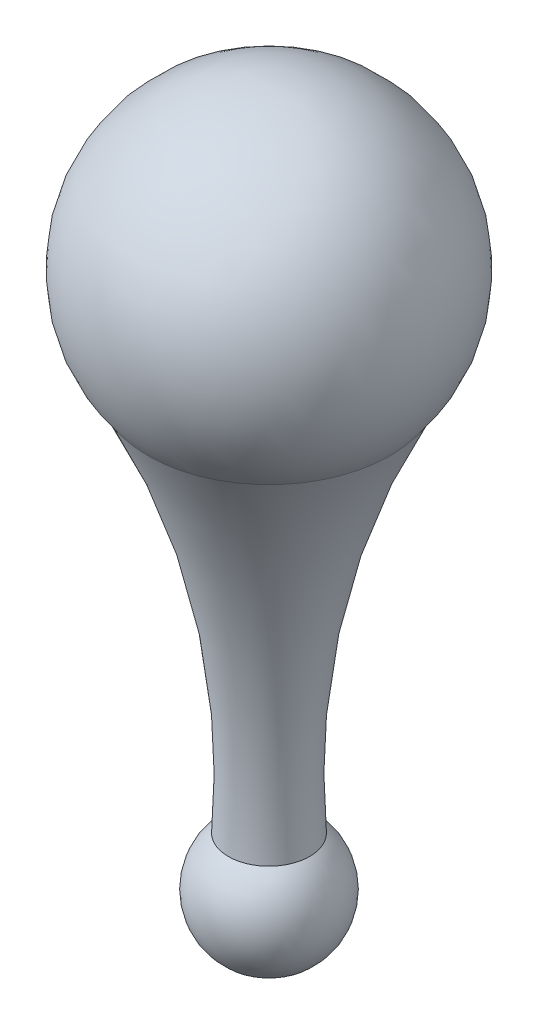
SolidWorks part; units mm, degrees
ref_plane "Front Plane" through (0, 0, 0) normal (0, 0, 1) x (1, 0, 0)
ref_plane "Top Plane" through (0, 0, 0) normal (0, 1, 0) x (1, 0, 0)
ref_plane "Right Plane" through (0, 0, 0) normal (1, 0, 0) x (0, 0, -1)
sketch "Sketch1" plane through (0, 0, 0) normal (0, 0, 1) x (1, 0, 0)
  line L0 (0, 127) -> (0, -127)
  line L1 (0, -127) -> (0, -381)
  line L2 (0, -381) -> (0, -482.6)
  line L3 (0, -431.8) -> (32.6536, -392.8849) construction
  line L4 (0, 0) -> (97.2876, -81.634) construction
  arc A0 (97.2876, -81.634) -> (0, 127) centre (0, 0) ccw
  arc A1 (0, 127) -> (0, -127) centre (0, 0) ccw construction
  arc A3 (0, -482.6) -> (32.6536, -392.8849) centre (0, -431.8) ccw
  arc A4 (0, -381) -> (0, -482.6) centre (0, -431.8) ccw construction
  arc A5 (32.6536, -392.8849) -> (97.2876, -81.634) centre (615.3901, -351.559) cw
  arc A6 (0, -127) -> (97.2876, -81.634) centre (0, 0) ccw construction
  arc A7 (32.6536, -392.8849) -> (0, -381) centre (0, -431.8) ccw construction
  point P9 (0, 0)
  point P11 (97.2876, -85.239)
  dimension "D1" = 254
  dimension "D2" = 101.6
  dimension "D5" = 584.2
  dimension "D3" = 40
  dimension "D4" = 50
  dimension "D6" = 431.8
revolve "Revolve1" add sketch "Sketch1" angle 360 about L0
